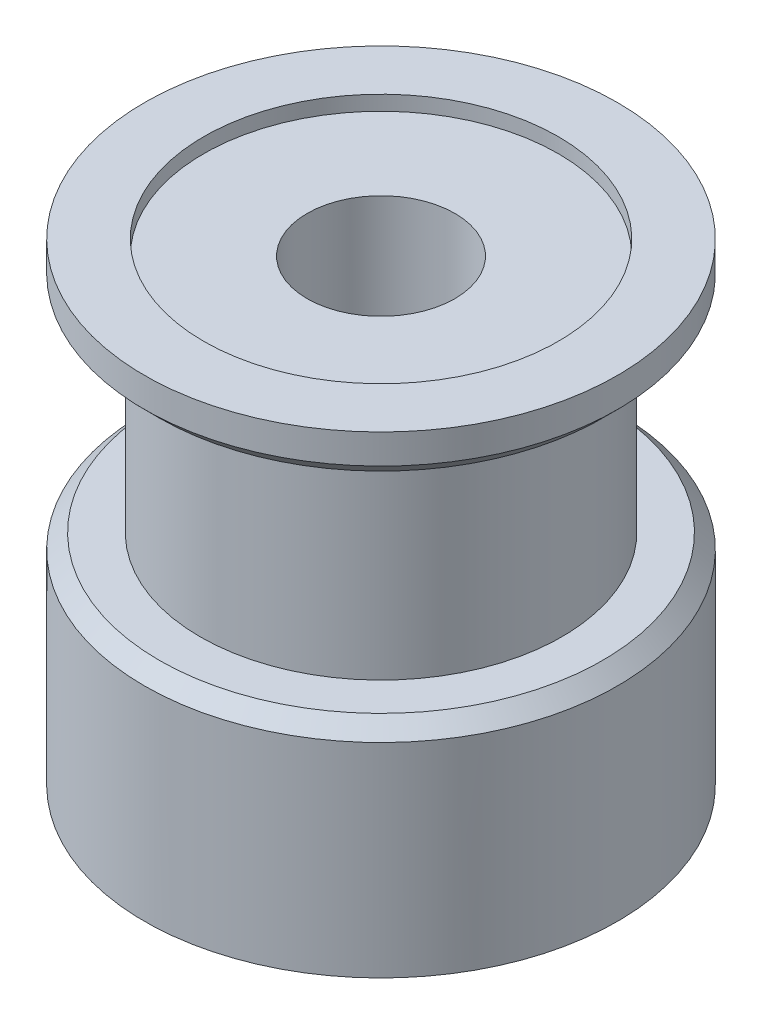
SolidWorks part; units mm, degrees
material "1060 Alloy"
ref_plane "Front Plane" through (0, 0, 0) normal (0, 0, 1) x (1, 0, 0)
ref_plane "Top Plane" through (0, 0, 0) normal (0, 1, 0) x (1, 0, 0)
ref_plane "Right Plane" through (0, 0, 0) normal (1, 0, 0) x (0, 0, -1)
sketch "Sketch1" plane through (0, 0, 0) normal (0, 0, 1) x (1, 0, 0)
  line L8 (0, 0) -> (0, 46.0732) construction
  line L9 (2.5, 0) -> (2.5, 16)
  line L10 (2.5, 16) -> (8, 16)
  line L11 (8, 16) -> (8, 14.5)
  line L12 (8, 14.5) -> (6.12, 14.5)
  line L13 (6.12, 14.5) -> (6.12, 7.4)
  line L14 (6.12, 7.4) -> (8, 7.4)
  line L15 (8, 7.4) -> (8, 0)
  line L16 (8, 0) -> (2.5, 0)
  dimension "D1" = 5
  dimension "D2" = 16
  dimension "D3" = 7.1
  dimension "D4" = 7.4
  dimension "D5" = 12.24
  dimension "D6" = 16
revolve "Revolve1" add sketch "Sketch1" angle 360 about L8
chamfer "Chamfer1" distance 0.5 angle 45 2 edges at (0, 14.5, -8) (0, 7.4, -8)
sketch "Sketch2" plane through (0, 16, 0) normal (0, 1, 0) x (1, 0, 0)
  circle A0 centre (0, 0) radius 6
  dimension "D1" = 12
extrude "Cut-Extrude1" cut sketch "Sketch2" against normal blind 0.5
